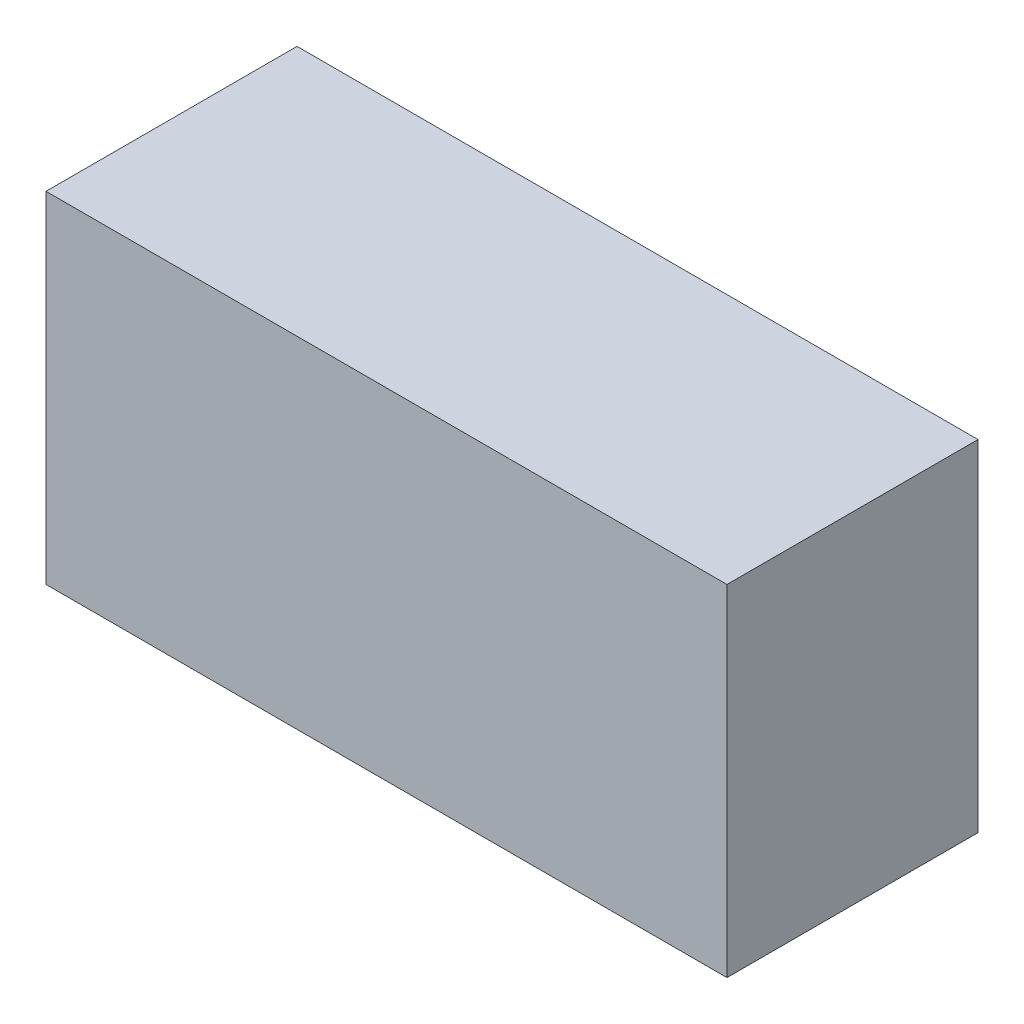
SolidWorks part; units mm, degrees
ref_plane "Front Plane" through (0, 0, 0) normal (0, 0, 1) x (1, 0, 0)
ref_plane "Top Plane" through (0, 0, 0) normal (0, 1, 0) x (1, 0, 0)
ref_plane "Right Plane" through (0, 0, 0) normal (1, 0, 0) x (0, 0, -1)
sketch "Sketch1" plane through (0, 0, 0) normal (0, 0, 1) x (1, 0, 0)
  line L1 (-29.972, 14.986) -> (29.972, 14.986)
  line L2 (-29.972, 14.986) -> (-29.972, -14.986)
  line L3 (-29.972, -14.986) -> (29.972, -14.986)
  line L4 (29.972, 14.986) -> (29.972, -14.986)
  line L5 (-29.972, 14.986) -> (29.972, -14.986) construction
  line L6 (-29.972, -14.986) -> (29.972, 14.986) construction
  point P0 (0, 0)
  dimension "D1" = 59.944
  dimension "D2" = 29.972
extrude "Boss-Extrude1" add sketch "Sketch1" along normal blind 22.098
